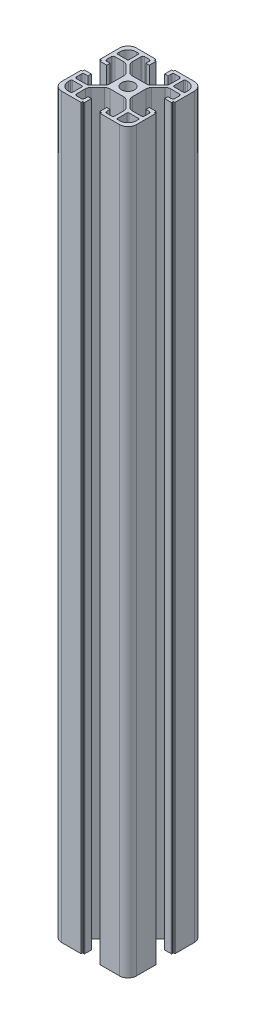
SolidWorks part; units mm, degrees
ref_plane "Front Plane" through (0, 0, 0) normal (0, 0, 1) x (1, 0, 0)
ref_plane "Top Plane" through (0, 0, 0) normal (0, 1, 0) x (1, 0, 0)
ref_plane "Right Plane" through (0, 0, 0) normal (1, 0, 0) x (0, 0, -1)
sketch "Sketch1" plane through (0, 0, 0) normal (0, 1, 0) x (1, 0, 0)
  line L0 (84.1702, 31.7204) -> (84.1702, 42.1204)
  line L1 (44.1702, 62.7204) -> (44.1702, 52.3204)
  line L2 (48.6702, 27.2204) -> (59.0702, 27.2204)
  line L3 (79.6702, 67.2204) -> (69.4702, 67.2204)
  line L4 (84.1702, 52.3204) -> (84.1702, 62.7204)
  line L5 (58.8702, 67.2204) -> (48.6702, 67.2204)
  line L6 (44.1702, 42.1204) -> (44.1702, 31.7204)
  line L7 (69.2702, 27.2204) -> (79.6702, 27.2204)
  line L10 (44.1702, 42.1204) -> (44.7702, 42.1204)
  line L11 (44.9702, 42.3204) -> (44.9702, 42.9204)
  line L12 (48.6702, 43.1204) -> (45.1702, 43.1204)
  line L13 (48.6702, 41.3204) -> (48.6702, 43.1204)
  line L14 (46.9702, 41.3204) -> (48.6702, 41.3204)
  line L15 (45.9702, 37.9704) -> (45.9702, 40.3204)
  line L16 (51.6169, 36.9704) -> (46.9702, 36.9704)
  line L17 (57.2915, 41.4024) -> (53.7382, 37.8491)
  line L18 (58.1702, 50.9171) -> (58.1702, 43.5237)
  line L19 (53.7382, 56.5917) -> (57.2915, 53.0384)
  line L20 (46.9702, 57.4704) -> (51.6169, 57.4704)
  line L21 (45.9702, 54.1204) -> (45.9702, 56.4704)
  line L22 (48.6702, 53.1204) -> (46.9702, 53.1204)
  line L23 (48.6702, 51.3204) -> (48.6702, 53.1204)
  line L24 (45.1702, 51.3204) -> (48.6702, 51.3204)
  line L25 (44.9702, 51.5204) -> (44.9702, 52.1204)
  line L26 (44.7702, 52.3204) -> (44.1702, 52.3204)
  line L29 (59.0702, 67.0204) -> (59.0702, 66.6204)
  line L30 (59.2702, 66.4204) -> (59.8702, 66.4204)
  line L31 (60.0702, 62.7204) -> (60.0702, 66.2204)
  line L32 (58.2702, 62.7204) -> (60.0702, 62.7204)
  line L33 (58.2702, 64.4204) -> (58.2702, 62.7204)
  line L34 (54.9202, 65.4204) -> (57.2702, 65.4204)
  line L35 (53.9202, 59.7737) -> (53.9202, 64.4204)
  line L36 (58.3522, 54.0991) -> (54.7989, 57.6524)
  line L37 (67.8669, 53.2204) -> (60.4735, 53.2204)
  line L38 (73.5415, 57.6524) -> (69.9882, 54.0991)
  line L39 (74.4202, 64.4204) -> (74.4202, 59.7737)
  line L40 (71.0702, 65.4204) -> (73.4202, 65.4204)
  line L41 (70.0702, 62.7204) -> (70.0702, 64.4204)
  line L42 (68.2702, 62.7204) -> (70.0702, 62.7204)
  line L43 (68.2702, 66.2204) -> (68.2702, 62.7204)
  line L44 (68.4702, 66.4204) -> (69.0702, 66.4204)
  line L45 (69.2702, 66.6204) -> (69.2702, 67.0204)
  line L48 (84.1702, 52.3204) -> (83.5702, 52.3204)
  line L49 (83.3702, 52.1204) -> (83.3702, 51.5204)
  line L50 (79.6702, 51.3204) -> (83.1702, 51.3204)
  line L51 (79.6702, 53.1204) -> (79.6702, 51.3204)
  line L52 (81.3702, 53.1204) -> (79.6702, 53.1204)
  line L53 (82.3702, 56.4704) -> (82.3702, 54.1204)
  line L54 (76.7235, 57.4704) -> (81.3702, 57.4704)
  line L55 (71.0489, 53.0384) -> (74.6022, 56.5917)
  line L56 (70.1702, 43.5237) -> (70.1702, 50.9171)
  line L57 (74.6022, 37.8491) -> (71.0489, 41.4024)
  line L58 (81.3702, 36.9704) -> (76.7235, 36.9704)
  line L59 (82.3702, 40.3204) -> (82.3702, 37.9704)
  line L60 (79.6702, 41.3204) -> (81.3702, 41.3204)
  line L61 (79.6702, 43.1204) -> (79.6702, 41.3204)
  line L62 (83.1702, 43.1204) -> (79.6702, 43.1204)
  line L63 (83.3702, 42.9204) -> (83.3702, 42.3204)
  line L64 (83.5702, 42.1204) -> (84.1702, 42.1204)
  line L67 (69.2702, 27.2204) -> (69.2702, 27.8204)
  line L68 (69.0702, 28.0204) -> (68.4702, 28.0204)
  line L69 (68.2702, 31.7204) -> (68.2702, 28.2204)
  line L70 (70.0702, 31.7204) -> (68.2702, 31.7204)
  line L71 (70.0702, 30.0204) -> (70.0702, 31.7204)
  line L72 (73.4202, 29.0204) -> (71.0702, 29.0204)
  line L73 (74.4202, 34.6671) -> (74.4202, 30.0204)
  line L74 (69.9882, 40.3417) -> (73.5415, 36.7884)
  line L75 (60.4735, 41.2204) -> (67.8669, 41.2204)
  line L76 (54.7989, 36.7884) -> (58.3522, 40.3417)
  line L77 (53.9202, 30.0204) -> (53.9202, 34.6671)
  line L78 (57.2702, 29.0204) -> (54.9202, 29.0204)
  line L79 (58.2702, 31.7204) -> (58.2702, 30.0204)
  line L80 (60.0702, 31.7204) -> (58.2702, 31.7204)
  line L81 (60.0702, 28.2204) -> (60.0702, 31.7204)
  line L82 (59.8702, 28.0204) -> (59.2702, 28.0204)
  line L83 (59.0702, 27.8204) -> (59.0702, 27.2204)
  line L84 (82.3702, 34.6704) -> (82.3702, 33.5204)
  line L85 (76.7202, 35.1704) -> (81.8702, 35.1704)
  line L86 (76.2202, 29.5204) -> (76.2202, 34.6704)
  line L87 (77.8702, 29.0204) -> (76.7202, 29.0204)
  line L88 (51.6202, 29.0204) -> (50.4702, 29.0204)
  line L89 (52.1202, 34.6704) -> (52.1202, 29.5204)
  line L90 (46.4702, 35.1704) -> (51.6202, 35.1704)
  line L91 (45.9702, 33.5204) -> (45.9702, 34.6704)
  line L92 (45.9702, 59.7704) -> (45.9702, 60.9204)
  line L93 (51.6202, 59.2704) -> (46.4702, 59.2704)
  line L94 (52.1202, 64.9204) -> (52.1202, 59.7704)
  line L95 (50.4702, 65.4204) -> (51.6202, 65.4204)
  line L96 (76.7202, 65.4204) -> (77.8702, 65.4204)
  line L97 (76.2202, 59.7704) -> (76.2202, 64.9204)
  line L98 (81.8702, 59.2704) -> (76.7202, 59.2704)
  line L99 (82.3702, 60.9204) -> (82.3702, 59.7704)
  arc A0 (60.7702, 47.2204) -> (67.5702, 47.2204) centre (64.1702, 47.2204) ccw
  arc A1 (44.1702, 31.7204) -> (48.6702, 27.2204) centre (48.6702, 31.7204) ccw
  arc A2 (44.7702, 42.1204) -> (44.9702, 42.3204) centre (44.7702, 42.3204) ccw
  arc A3 (45.1702, 43.1204) -> (44.9702, 42.9204) centre (45.1702, 42.9204) ccw
  arc A4 (46.9702, 41.3204) -> (45.9702, 40.3204) centre (46.9702, 40.3204) ccw
  arc A5 (45.9702, 37.9704) -> (46.9702, 36.9704) centre (46.9702, 37.9704) ccw
  arc A6 (51.6169, 36.9704) -> (53.7382, 37.8491) centre (51.6169, 39.9704) ccw
  arc A7 (57.2915, 41.4024) -> (58.1702, 43.5237) centre (55.1702, 43.5237) ccw
  arc A8 (58.1702, 50.9171) -> (57.2915, 53.0384) centre (55.1702, 50.9171) ccw
  arc A9 (53.7382, 56.5917) -> (51.6169, 57.4704) centre (51.6169, 54.4704) ccw
  arc A10 (46.9702, 57.4704) -> (45.9702, 56.4704) centre (46.9702, 56.4704) ccw
  arc A11 (45.9702, 54.1204) -> (46.9702, 53.1204) centre (46.9702, 54.1204) ccw
  arc A12 (44.9702, 51.5204) -> (45.1702, 51.3204) centre (45.1702, 51.5204) ccw
  arc A13 (44.9702, 52.1204) -> (44.7702, 52.3204) centre (44.7702, 52.1204) ccw
  arc A14 (48.6702, 67.2204) -> (44.1702, 62.7204) centre (48.6702, 62.7204) ccw
  arc A15 (59.0702, 67.0204) -> (58.8702, 67.2204) centre (58.8702, 67.0204) ccw
  arc A16 (59.0702, 66.6204) -> (59.2702, 66.4204) centre (59.2702, 66.6204) ccw
  arc A17 (60.0702, 66.2204) -> (59.8702, 66.4204) centre (59.8702, 66.2204) ccw
  arc A18 (58.2702, 64.4204) -> (57.2702, 65.4204) centre (57.2702, 64.4204) ccw
  arc A19 (54.9202, 65.4204) -> (53.9202, 64.4204) centre (54.9202, 64.4204) ccw
  arc A20 (53.9202, 59.7737) -> (54.7989, 57.6524) centre (56.9202, 59.7737) ccw
  arc A21 (58.3522, 54.0991) -> (60.4735, 53.2204) centre (60.4735, 56.2204) ccw
  arc A22 (67.8669, 53.2204) -> (69.9882, 54.0991) centre (67.8669, 56.2204) ccw
  arc A23 (73.5415, 57.6524) -> (74.4202, 59.7737) centre (71.4202, 59.7737) ccw
  arc A24 (74.4202, 64.4204) -> (73.4202, 65.4204) centre (73.4202, 64.4204) ccw
  arc A25 (71.0702, 65.4204) -> (70.0702, 64.4204) centre (71.0702, 64.4204) ccw
  arc A26 (68.4702, 66.4204) -> (68.2702, 66.2204) centre (68.4702, 66.2204) ccw
  arc A27 (69.0702, 66.4204) -> (69.2702, 66.6204) centre (69.0702, 66.6204) ccw
  arc A28 (69.4702, 67.2204) -> (69.2702, 67.0204) centre (69.4702, 67.0204) ccw
  arc A29 (84.1702, 62.7204) -> (79.6702, 67.2204) centre (79.6702, 62.7204) ccw
  arc A30 (83.5702, 52.3204) -> (83.3702, 52.1204) centre (83.5702, 52.1204) ccw
  arc A31 (83.1702, 51.3204) -> (83.3702, 51.5204) centre (83.1702, 51.5204) ccw
  arc A32 (81.3702, 53.1204) -> (82.3702, 54.1204) centre (81.3702, 54.1204) ccw
  arc A33 (82.3702, 56.4704) -> (81.3702, 57.4704) centre (81.3702, 56.4704) ccw
  arc A34 (76.7235, 57.4704) -> (74.6022, 56.5917) centre (76.7235, 54.4704) ccw
  arc A35 (71.0489, 53.0384) -> (70.1702, 50.9171) centre (73.1702, 50.9171) ccw
  arc A36 (70.1702, 43.5237) -> (71.0489, 41.4024) centre (73.1702, 43.5237) ccw
  arc A37 (74.6022, 37.8491) -> (76.7235, 36.9704) centre (76.7235, 39.9704) ccw
  arc A38 (81.3702, 36.9704) -> (82.3702, 37.9704) centre (81.3702, 37.9704) ccw
  arc A39 (82.3702, 40.3204) -> (81.3702, 41.3204) centre (81.3702, 40.3204) ccw
  arc A40 (83.3702, 42.9204) -> (83.1702, 43.1204) centre (83.1702, 42.9204) ccw
  arc A41 (83.3702, 42.3204) -> (83.5702, 42.1204) centre (83.5702, 42.3204) ccw
  arc A42 (79.6702, 27.2204) -> (84.1702, 31.7204) centre (79.6702, 31.7204) ccw
  arc A43 (69.2702, 27.8204) -> (69.0702, 28.0204) centre (69.0702, 27.8204) ccw
  arc A44 (68.2702, 28.2204) -> (68.4702, 28.0204) centre (68.4702, 28.2204) ccw
  arc A45 (70.0702, 30.0204) -> (71.0702, 29.0204) centre (71.0702, 30.0204) ccw
  arc A46 (73.4202, 29.0204) -> (74.4202, 30.0204) centre (73.4202, 30.0204) ccw
  arc A47 (74.4202, 34.6671) -> (73.5415, 36.7884) centre (71.4202, 34.6671) ccw
  arc A48 (69.9882, 40.3417) -> (67.8669, 41.2204) centre (67.8669, 38.2204) ccw
  arc A49 (60.4735, 41.2204) -> (58.3522, 40.3417) centre (60.4735, 38.2204) ccw
  arc A50 (54.7989, 36.7884) -> (53.9202, 34.6671) centre (56.9202, 34.6671) ccw
  arc A51 (53.9202, 30.0204) -> (54.9202, 29.0204) centre (54.9202, 30.0204) ccw
  arc A52 (57.2702, 29.0204) -> (58.2702, 30.0204) centre (57.2702, 30.0204) ccw
  arc A53 (59.8702, 28.0204) -> (60.0702, 28.2204) centre (59.8702, 28.2204) ccw
  arc A54 (59.2702, 28.0204) -> (59.0702, 27.8204) centre (59.2702, 27.8204) ccw
  arc A55 (82.3702, 34.6704) -> (81.8702, 35.1704) centre (81.8702, 34.6704) ccw
  arc A56 (76.7202, 35.1704) -> (76.2202, 34.6704) centre (76.7202, 34.6704) ccw
  arc A57 (76.2202, 29.5204) -> (76.7202, 29.0204) centre (76.7202, 29.5204) ccw
  arc A58 (77.8702, 29.0204) -> (82.3702, 33.5204) centre (77.8702, 33.5204) ccw
  arc A59 (51.6202, 29.0204) -> (52.1202, 29.5204) centre (51.6202, 29.5204) ccw
  arc A60 (52.1202, 34.6704) -> (51.6202, 35.1704) centre (51.6202, 34.6704) ccw
  arc A61 (46.4702, 35.1704) -> (45.9702, 34.6704) centre (46.4702, 34.6704) ccw
  arc A62 (45.9702, 33.5204) -> (50.4702, 29.0204) centre (50.4702, 33.5204) ccw
  arc A63 (45.9702, 59.7704) -> (46.4702, 59.2704) centre (46.4702, 59.7704) ccw
  arc A64 (51.6202, 59.2704) -> (52.1202, 59.7704) centre (51.6202, 59.7704) ccw
  arc A65 (52.1202, 64.9204) -> (51.6202, 65.4204) centre (51.6202, 64.9204) ccw
  arc A66 (50.4702, 65.4204) -> (45.9702, 60.9204) centre (50.4702, 60.9204) ccw
  arc A67 (76.7202, 65.4204) -> (76.2202, 64.9204) centre (76.7202, 64.9204) ccw
  arc A68 (76.2202, 59.7704) -> (76.7202, 59.2704) centre (76.7202, 59.7704) ccw
  arc A69 (81.8702, 59.2704) -> (82.3702, 59.7704) centre (81.8702, 59.7704) ccw
  arc A70 (82.3702, 60.9204) -> (77.8702, 65.4204) centre (77.8702, 60.9204) ccw
  arc A71 (67.5702, 47.2204) -> (60.7702, 47.2204) centre (64.1702, 47.2204) ccw
extrude "Boss-Extrude1" add sketch "Sketch1" along normal blind 394.54
